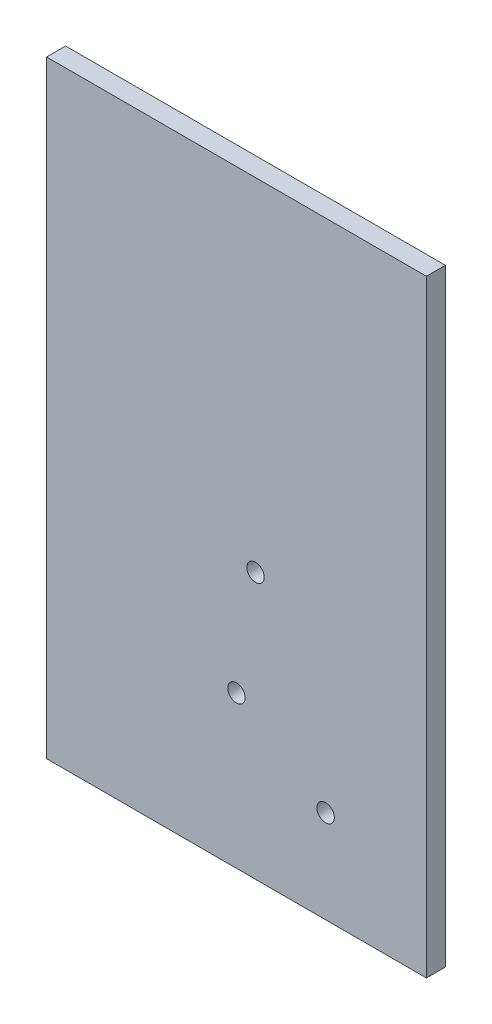
SolidWorks part; units mm, degrees
ref_plane "Front Plane" through (0, 0, 0) normal (0, 0, 1) x (1, 0, 0)
ref_plane "Top Plane" through (0, 0, 0) normal (0, 1, 0) x (1, 0, 0)
ref_plane "Right Plane" through (0, 0, 0) normal (1, 0, 0) x (0, 0, -1)
sketch "Sketch1" plane through (0, 0, 0) normal (0, 0, 1) x (1, 0, 0)
  line L0 (-57.7606, -157.9694) -> (56.5394, -157.9694)
  line L1 (-64.1106, 38.8806) -> (62.8894, 38.8806)
  line L2 (-64.1106, 38.8806) -> (-64.1106, -164.3194)
  line L3 (-64.1106, -164.3194) -> (62.8894, -164.3194)
  line L4 (62.8894, 38.8806) -> (62.8894, -164.3194)
  line L5 (56.5394, 32.5306) -> (56.5394, -157.9694)
  line L6 (-57.7606, 32.5306) -> (56.5394, 32.5306)
  line L7 (-57.7606, 32.5306) -> (-57.7606, -157.9694)
  line L8 (-0.6106, -157.9694) -> (-0.6106, -113.5194)
  line L9 (-0.6106, -113.5194) -> (-57.7606, -113.5194)
  line L10 (-0.6106, -113.5194) -> (29.182, -113.5194)
  line L11 (29.182, -113.5194) -> (29.182, -133.3087)
  line L12 (-0.6106, -113.5194) -> (-0.6106, -75.4194)
  line L13 (-0.6106, -75.4194) -> (5.7394, -75.4194)
  circle A0 centre (-0.6106, -113.5194) radius 2.921
  circle A1 centre (29.182, -133.3087) radius 2.921
  circle A2 centre (5.7394, -75.4194) radius 2.921
  dimension "D6" = 5.842
  dimension "D7" = 5.842
  dimension "D8" = 5.842
  dimension "D1" = 127
  dimension "D2" = 203.2
  dimension "D4" = 57.15
  dimension "D5" = 44.45
  dimension "D9" = 6.35
  dimension "D10" = 38.1
  dimension "D3" = 6.35
extrude "Boss-Extrude2" add sketch "Sketch1" along normal blind 6.35
